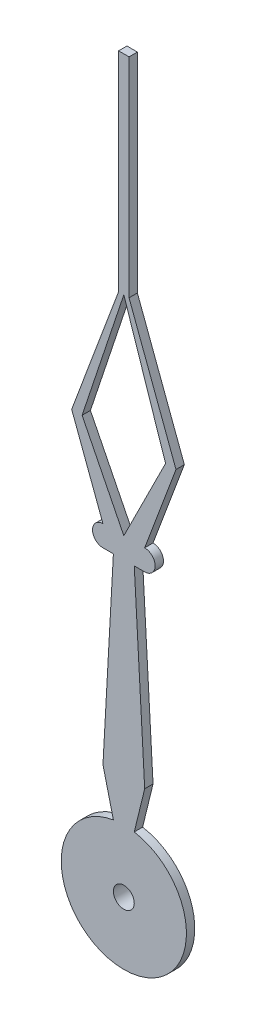
SolidWorks part; units mm, degrees
ref_plane "Front Plane" through (0, 0, 0) normal (0, 0, 1) x (1, 0, 0)
ref_plane "Top Plane" through (0, 0, 0) normal (0, 1, 0) x (1, 0, 0)
ref_plane "Right Plane" through (0, 0, 0) normal (1, 0, 0) x (0, 0, -1)
sketch "Croquis1" plane through (0, 0, 0) normal (0, 0, 1) x (1, 0, 0)
  line L1 (-0.5, 7) -> (-0.25, 7)
  line L3 (0.25, 7) -> (0.5, 7)
  line L4 (-0.25, 1.479) -> (-0.5, 2.5)
  line L6 (-0.5, 2.5) -> (-0.25, 7)
  line L7 (0.25, 7) -> (0.5, 2.5)
  line L8 (0.5, 2.5) -> (0.25, 1.479)
  line L11 (-0.5, 7.5) -> (-1.25, 9.5)
  line L12 (0, 7.5) -> (-1, 9.5)
  line L13 (0.5, 7.5) -> (1.25, 9.5)
  line L14 (0, 7.5) -> (1, 9.5)
  line L16 (1.25, 9.5) -> (0.125, 12.5)
  line L17 (-1, 9.5) -> (0, 12.5)
  line L18 (0, 12.5) -> (1, 9.5)
  line L19 (-1.25, 9.5) -> (-0.125, 12.5)
  line L20 (0.125, 12.5) -> (0.125, 17.5)
  line L21 (0.125, 17.5) -> (-0.125, 17.5)
  line L22 (-0.125, 17.5) -> (-0.125, 12.5)
  arc A0 (-0.25, 1.479) -> (0.25, 1.479) centre (0, 0) ccw
  circle A1 centre (0, 0) radius 0.25
  arc A2 (-0.5, 7) -> (-0.5, 7.5) centre (-0.5, 7.25) cw
  arc A3 (0.5, 7) -> (0.5, 7.5) centre (0.5, 7.25) ccw
  dimension "D11" = 0.5
  dimension "D10" = 0.25
  dimension "D23" = 3
  dimension "D21" = 0.5
  dimension "D3" = 1
  dimension "D4" = 0.25
  dimension "D5" = 0.5
  dimension "D6" = 2.5
  dimension "D7" = 4.5
  dimension "D8" = 0.5
  dimension "D9" = 0.25
  dimension "D12" = 2
  dimension "D13" = 1
  dimension "D14" = 1
  dimension "D15" = 0.5
  dimension "D16" = 3
  dimension "D17" = 0.25
  dimension "D18" = 0.25
  dimension "D19" = 0.125
  dimension "D20" = 0.125
  dimension "D22" = 5
extrude "Saliente-Extruir1" add sketch "Croquis1" along normal blind 0.2
sketch "Croquis2" plane through (0, 0, 0) normal (0, 0, -1) x (-1, 0, 0)
  circle A0 centre (0, 0) radius 0.25 construction
  circle A1 centre (0, 0) radius 0.25
  circle A2 centre (0, 0) radius 0.5
  dimension "D1" = 1
extrude "Saliente-Extruir2" add sketch "Croquis2" along normal blind 0.2
